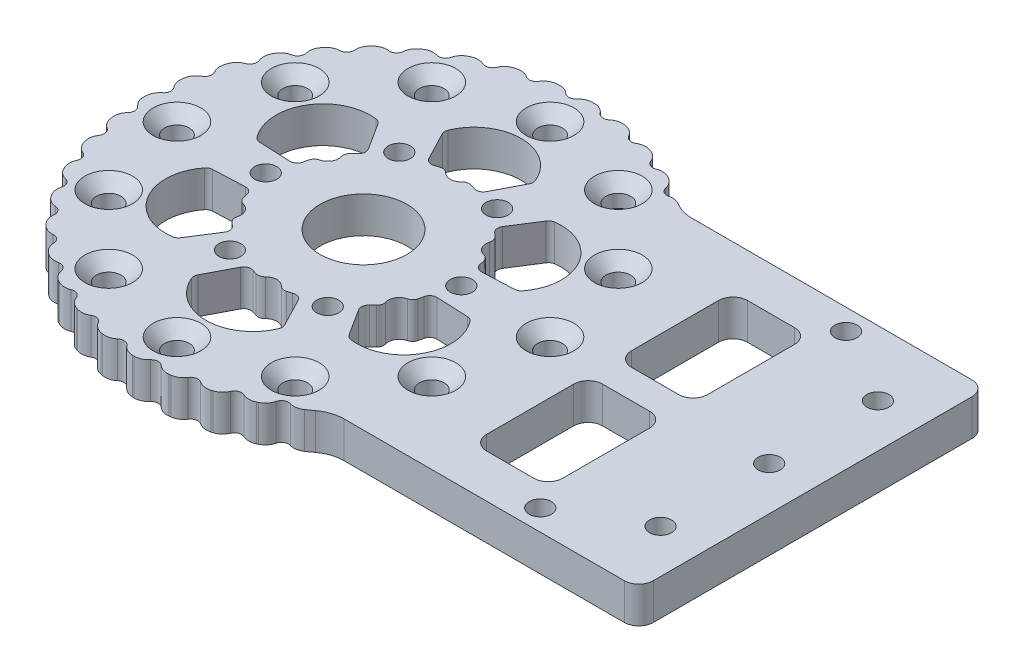
SolidWorks part; units mm, degrees
material "Thornel Mat VMA"
ref_plane "前视基准面" through (0, 0, 0) normal (0, 0, 1) x (1, 0, 0)
ref_plane "上视基准面" through (0, 0, 0) normal (0, 1, 0) x (1, 0, 0)
ref_plane "右视基准面" through (0, 0, 0) normal (1, 0, 0) x (0, 0, -1)
other "Configuration Table"
sketch "草图1" plane through (0, 0, 0) normal (0, 1, 0) x (1, 0, 0)
  line L1 (-105, -24) -> (105, -24)
  line L2 (-105, -24) -> (-105, 24) construction
  line L3 (-105, 24) -> (105, 24)
  line L4 (105, -24) -> (105, 24)
  line L5 (-105, -24) -> (105, 24) construction
  line L6 (-105, 24) -> (105, -24) construction
  circle A0 centre (105, 0) radius 24
  circle A1 centre (-105, 0) radius 37
  point P0 (0, 0)
  dimension "D1" = 48
  dimension "D3" = 74
  dimension "D2" = 210
extrude "凸台-拉伸1" add sketch "草图1" along normal blind 5
sketch "草图2" plane through (0, 0, 0) normal (0, -1, 0) x (1, 0, 0)
  line L0 (118.435, 13.435) -> (105, 0) construction
  line L1 (105, 0) -> (129, 0) construction
  circle A0 centre (105, 0) radius 19 construction
  circle A1 centre (118.435, 13.435) radius 1.275
  arc A2 (105, -24) -> (105, 24) centre (105, 0) ccw construction
  circle A3 centre (118.435, -13.435) radius 1.275
  circle A4 centre (91.565, -13.435) radius 1.275
  circle A5 centre (91.565, 13.435) radius 1.275
  circle A6 centre (124, 0) radius 1.275
  circle A7 centre (105, -19) radius 1.275
  circle A8 centre (86, 0) radius 1.275
  circle A9 centre (105, 19) radius 1.275
  point P18 (105, 0)
  point P26 (105, 0)
  dimension "D1" = 38
  dimension "D3" = 2.55
  dimension "D4" = 4
  dimension "D2" = 45
  dimension "D5" = 4
extrude "切除-拉伸1" cut sketch "草图2" against normal through all
sketch "草图3" plane through (0, 5, 0) normal (0, 1, 0) x (1, 0, 0)
  circle A16 centre (-105, 0) radius 17.25 construction
  circle A17 centre (-105, 17.25) radius 2.025
  circle A18 centre (-90.0611, 8.625) radius 2.025
  circle A19 centre (-90.0611, -8.625) radius 2.025
  circle A20 centre (-105, -17.25) radius 2.025
  circle A21 centre (-119.9389, -8.625) radius 2.025
  circle A22 centre (-119.9389, 8.625) radius 2.025
  point P18 (-105, 0)
  dimension "D1" = 34.5
  dimension "D2" = 4.05
sketch "草图5" plane through (0, 5, 0) normal (0, 1, 0) x (1, 0, 0)
  circle A0 centre (-105, 0) radius 10
  dimension "D1" = 20
extrude "切除-拉伸3" cut sketch "草图5" against normal through all
sketch "草图6" plane through (0, 5, 0) normal (0, 1, 0) x (1, 0, 0)
  circle A0 centre (-105, 0) radius 30 construction
  circle A1 centre (-135, 0) radius 1.525
  circle A2 centre (-120, 25.9808) radius 1.525
  circle A3 centre (-90, 25.9808) radius 1.525
  circle A4 centre (-75, 0) radius 1.525
  circle A5 centre (-90, -25.9808) radius 1.525
  circle A6 centre (-120, -25.9808) radius 1.525
  point P17 (-105, 0)
  dimension "D1" = 60
  dimension "D2" = 3.05
  dimension "D3" = 6
extrude "切除-拉伸4" cut sketch "草图6" against normal through all
sketch "草图7" plane through (0, 5, 0) normal (0, 1, 0) x (1, 0, 0)
  line L0 (-76.8397, 24) -> (105, 24) construction
  line L1 (0, 0) -> (50000, 0) construction
  circle A0 centre (-60, 19) radius 1.525
  circle A1 centre (-27, 19) radius 1.525
  circle A2 centre (6, 19) radius 1.525
  circle A3 centre (39, 19) radius 1.525
  circle A4 centre (72, 19) radius 1.525
  circle A5 centre (72, -19) radius 1.525
  circle A6 centre (39, -19) radius 1.525
  circle A7 centre (6, -19) radius 1.525
  circle A8 centre (-27, -19) radius 1.525
  circle A9 centre (-60, -19) radius 1.525
  dimension "D1" = 3.05
  dimension "D2" = 5
  dimension "D3" = 60
  dimension "D5" = 33
  dimension "D4" = 5
sketch "草图8" plane through (0, 0, 0) normal (0, -1, 0) x (1, 0, 0)
  line L0 (-44.8493, 17.0002) -> (-34.9998, 17.0002) construction
  line L1 (-32.9998, -3.6043) -> (-32.9998, 15.0002) construction
  line L2 (-46.6169, 14.0644) -> (-36.7674, -4.5401) construction
  line L3 (-48.9998, -16.9998) -> (-39.1504, -16.9998) construction
  line L5 (-47.2322, 4.5405) -> (-37.3828, -14.064) construction
  line L6 (-50.9998, -14.9998) -> (-50.9998, 3.6048) construction
  line L7 (-44.8493, 17.0002) -> (-34.9998, 17.0002)
  line L13 (-32.9998, -3.6043) -> (-32.9998, 15.0002)
  line L14 (-46.6169, 14.0644) -> (-36.7674, -4.5401)
  line L15 (-48.9998, -16.9998) -> (-39.1504, -16.9998)
  line L21 (-47.2322, 4.5405) -> (-37.3828, -14.064)
  line L22 (-50.9998, -14.9998) -> (-50.9998, 3.6048)
  arc A0 (-44.8493, 17.0002) -> (-46.6169, 14.0644) centre (-44.8493, 15.0002) ccw construction
  arc A1 (-32.9998, 15.0002) -> (-34.9998, 17.0002) centre (-34.9998, 15.0002) ccw construction
  arc A2 (-36.7674, -4.5401) -> (-32.9998, -3.6043) centre (-34.9998, -3.6043) ccw construction
  arc A3 (-39.1504, -16.9998) -> (-37.3828, -14.064) centre (-39.1504, -14.9998) ccw construction
  arc A36 (-50.9998, -14.9998) -> (-48.9998, -16.9998) centre (-48.9998, -14.9998) ccw construction
  arc A37 (-47.2322, 4.5405) -> (-50.9998, 3.6048) centre (-48.9998, 3.6048) ccw construction
  arc A38 (-44.8493, 17.0002) -> (-46.6169, 14.0644) centre (-44.8493, 15.0002) ccw
  arc A39 (-32.9998, 15.0002) -> (-34.9998, 17.0002) centre (-34.9998, 15.0002) ccw
  arc A40 (-36.7674, -4.5401) -> (-32.9998, -3.6043) centre (-34.9998, -3.6043) ccw
  arc A41 (-39.1504, -16.9998) -> (-37.3828, -14.064) centre (-39.1504, -14.9998) ccw
  arc A42 (-50.9998, -14.9998) -> (-48.9998, -16.9998) centre (-48.9998, -14.9998) ccw
  arc A43 (-47.2322, 4.5405) -> (-50.9998, 3.6048) centre (-48.9998, 3.6048) ccw
sketch "草图9" plane through (0, 0, 0) normal (0, -1, 0) x (1, 0, 0)
  circle A0 centre (105, 0) radius 12.5
  dimension "D1" = 25
extrude "切除-拉伸7" cut sketch "草图9" against normal through all
hole_wizard "M3 十字槽沉头木螺钉的锥形沉头孔1" positions "草图10" profile "草图11" countersink size "M3" standard "GB" end condition through all
sketch "草图10" plane through (0, 5, 0) normal (0, 1, 0) x (1, 0, 0)
  point P0 (105, 19)
sketch "草图11" plane through (105, 5, -19) normal (1, 0, 0) x (0, 0, 1)
  line L0 (0, 0) -> (0, 5)
  line L1 (0, 5) -> (1.8, 5)
  line L2 (1.8, 5) -> (1.8, 1.5)
  line L3 (1.8, 1.5) -> (3.3, 0)
  line L5 (3.3, 0) -> (0, 0)
  line L6 (-1.8, 1.5) -> (-3.3, 0) construction
  line L11 (0, -6.35) -> (0, 107.95) construction
  dimension "通孔孔直径" = 3.6
  dimension "通孔孔深度" = 5
  dimension "近端锥形沉头孔直径" = 6.6
  dimension "近端锥形沉头孔角度" = 90
hole_wizard "孔1" positions "草图12" profile "草图13" legacy end condition through all
sketch "草图12" plane through (0, 5, 0) normal (0, 1, 0) x (1, 0, 0)
  point P0 (91.565, 13.435)
  point P3 (86, 0)
  point P6 (91.565, -13.435)
  point P9 (105, -19)
  point P12 (118.435, -13.435)
  point P15 (124, 0)
  point P18 (118.435, 13.435)
sketch "草图13" plane through (91.565, 5, -13.435) normal (1, 0, 0) x (0, 0, 1)
  line L0 (0, 0) -> (0, 5)
  line L1 (0, 5) -> (1.5, 5)
  line L2 (1.5, 5) -> (1.5, 1.5)
  line L3 (1.5, 1.5) -> (3, 0)
  line L4 (3, 0) -> (0, 0)
  line L5 (0, -6.4453) -> (0, 115.525) construction
  line L6 (-1.5, 1.5) -> (-3, 0) construction
  dimension "直径" = 3
  dimension "深度" = 5
  dimension "锥坑角度" = 90
  dimension "锥坑直径" = 6
extrude "切除-拉伸8" cut sketch "草图3" against normal blind 10
sketch "草图14" plane through (0, 5, 0) normal (0, 1, 0) x (1, 0, 0)
  circle A0 centre (-105, 0) radius 37
  arc A1 (-76.8397, 24) -> (-76.8397, -24) centre (-105, 0) ccw construction
extrude "凸台-拉伸2" add sketch "草图14" against normal up to surface (5 mm away) up to face at (-105, 0, -15.225)
sketch "草图15" plane through (0, 5, 0) normal (0, 1, 0) x (1, 0, 0)
  circle A0 centre (-105, 0) radius 42.5
  dimension "D1" = 85
extrude "凸台-拉伸3" add sketch "草图15" against normal up to surface (5 mm away) up to face at (91.565, 0, -11.935)
sketch "草图16" plane through (0, 0, 0) normal (0, -1, 0) x (1, 0, 0)
  circle A0 centre (-105, 0) radius 13.5 construction
  circle A1 centre (-105, 13.5) radius 1.525
  circle A2 centre (-98.25, 11.6913) radius 1.525
  circle A3 centre (-93.3087, 6.75) radius 1.525
  circle A4 centre (-91.5, 0) radius 1.525
  circle A5 centre (-93.3087, -6.75) radius 1.525
  circle A6 centre (-98.25, -11.6913) radius 1.525
  circle A7 centre (-105, -13.5) radius 1.525
  circle A8 centre (-111.75, -11.6913) radius 1.525
  circle A9 centre (-116.6913, -6.75) radius 1.525
  circle A10 centre (-118.5, 0) radius 1.525
  circle A11 centre (-116.6913, 6.75) radius 1.525
  circle A12 centre (-111.75, 11.6913) radius 1.525
  point P22 (-105, 0)
  dimension "D1" = 27
  dimension "D2" = 3.05
  dimension "D3" = 12
extrude "切除-拉伸9" cut sketch "草图16" against normal up to surface (5 mm away) up to face at (4.1437, 5, 0)
sketch "草图18" plane through (0, 5, 0) normal (0, 1, 0) x (1, 0, 0)
  line L0 (-98.8153, 17.25) -> (-101.4581, 12.1732)
  line L1 (-111.1847, 17.25) -> (-108.5419, 12.1732)
  line L2 (-105, 0) -> (-105, -17.25) construction
  circle A0 centre (-105, 0) radius 17.25 construction
  circle A1 centre (-105, 17.25) radius 3.8 construction
  circle A2 centre (-90.0611, 8.625) radius 3.8 construction
  circle A3 centre (-90.0611, -8.625) radius 3.8 construction
  circle A4 centre (-105, -17.25) radius 3.8 construction
  circle A5 centre (-119.9389, -8.625) radius 3.8 construction
  circle A6 centre (-119.9389, 8.625) radius 3.8 construction
  arc A7 (-111.1847, 17.25) -> (-98.8153, 17.25) centre (-105, 15.25) cw
  arc A8 (-108.5419, 12.1732) -> (-101.4581, 12.1732) centre (-105, 5) cw
  point P17 (-105, 0)
  dimension "D1" = 34.5
  dimension "D2" = 7.6
  dimension "D5" = 6.5
  dimension "D7" = 8
  dimension "D4" = 2
  dimension "D6" = 5
  dimension "D8" = 55
  dimension "D3" = 6
extrude "切除-拉伸10" cut sketch "草图18" against normal up to surface (5 mm away) up to face at (-111.75, 0, -13.2163)
pattern_circular "阵列(圆周)1" count 6 over 360 about axis through (-105, 0, 0) along (0, 1, 0) of "切除-拉伸10"
sketch "草图19" plane through (0, 0, 0) normal (0, -1, 0) x (1, 0, 0)
  circle A0 centre (-105, 0) radius 6
  dimension "D1" = 12
extrude "切除-拉伸11" cut sketch "草图19" against normal up to surface (5 mm away) up to face at (-92.2475, 5, -7.3627)
sketch "草图20" plane through (0, 0, 0) normal (0, -1, 0) x (1, 0, 0)
  circle A10 centre (-105, 0) radius 36.75 construction
  circle A11 centre (-68.25, 0) radius 1.525
  circle A12 centre (-79.0138, -25.9862) radius 1.525
  circle A13 centre (-105, -36.75) radius 1.525
  circle A14 centre (-130.9862, -25.9862) radius 1.525
  circle A15 centre (-141.75, 0) radius 1.525
  circle A16 centre (-130.9862, 25.9862) radius 1.525
  circle A17 centre (-105, 36.75) radius 1.525
  circle A18 centre (-79.0138, 25.9862) radius 1.525
  point P21 (-105, 0)
  dimension "D1" = 73.5
  dimension "D2" = 3.05
fillet "圆角1" radius 2 2 edges at (-69.9251, 2.5, -24) (-69.9251, 2.5, 24)
sketch "草图21" plane through (0, 0, 0) normal (0, -1, 0) x (1, 0, 0)
  line L0 (-68.8856, -24) -> (105, -24) construction
  line L1 (-68.8856, 24) -> (105, 24) construction
  line L2 (-68.8856, -24) -> (105, -24)
  line L3 (-68.8856, 24) -> (105, 24)
  line L4 (-68.8856, 24) -> (-85.3786, 24)
  line L5 (-68.8856, -24) -> (-85.3786, -24)
  line L8 (105, 24) -> (-68.8856, 24)
  line L9 (-68.8856, -24) -> (105, -24)
  line L10 (105, 24) -> (-68.8856, 24)
  line L11 (-68.8856, -24) -> (105, -24)
  circle A0 centre (-105, 0) radius 31
  arc A3 (-70.5087, 24.8315) -> (-68.8856, 24) centre (-68.8856, 26) ccw
  arc A7 (-70.5087, 24.8315) -> (-68.8856, 24) centre (-68.8856, 26) ccw
  arc A8 (105, -24) -> (105, 24) centre (105, 0) ccw
  arc A12 (105, -24) -> (105, 24) centre (105, 0) ccw
  arc A13 (-70.5087, 24.8315) -> (-70.5087, -24.8315) centre (-105, 0) ccw
  arc A14 (-70.5087, 24.8315) -> (-70.5087, -24.8315) centre (-105, 0) ccw
  arc A15 (-68.8856, -24) -> (-70.5087, -24.8315) centre (-68.8856, -26) ccw
  arc A16 (-68.8856, -24) -> (-70.5087, -24.8315) centre (-68.8856, -26) ccw
  dimension "D1" = 62
  dimension "D2" = 0
extrude "切除-拉伸13" cut sketch "草图21" against normal through all contours A16 L5 A0 L4 A7 A14
fillet "圆角2" radius 1 36 edges at (-94.5436, 2.5, -7.6448) (-93.1512, 2.5, -5.2331) (-96.2286, 2.5, -9.154) (-93.1534, 2.5, -13.9811) (-86.9687, 2.5, -3.2689) (-92.6867, 2.5, -3.0193) (-93.1512, 2.5, 5.2331) (-94.5436, 2.5, 7.6448) (-92.6867, 2.5, 3.0193) (-86.9687, 2.5, 3.2689) (-93.1534, 2.5, 13.9811) (-96.2286, 2.5, 9.154) (-103.6077, 2.5, 12.8779) (-106.3923, 2.5, 12.8779) (-101.4581, 2.5, 12.1732) (-98.8153, 2.5, 17.25) (-111.1847, 2.5, 17.25) (-108.5419, 2.5, 12.1732) (-115.4564, 2.5, 7.6448) (-116.8488, 2.5, 5.2331) (-113.7714, 2.5, 9.154) (-123.0313, 2.5, 3.2689) (-117.3133, 2.5, 3.0193) (-116.8488, 2.5, -5.2331) (-115.4564, 2.5, -7.6448) (-117.3133, 2.5, -3.0193) (-123.0313, 2.5, -3.2689) (-116.8466, 2.5, -13.9811) (-113.7714, 2.5, -9.154) (-106.3923, 2.5, -12.8779) (-103.6077, 2.5, -12.8779) (-108.5419, 2.5, -12.1732) (-111.1847, 2.5, -17.25) (-98.8153, 2.5, -17.25) (-101.4581, 2.5, -12.1732) (-116.8466, 2.5, 13.9811)
sketch "草图22" plane through (0, 0, 0) normal (0, -1, 0) x (1, 0, 0)
  line L0 (-35, 24) -> (-35, -24)
  line L1 (-85.3786, 24) -> (105, 24) construction
  line L2 (-85.3786, -24) -> (105, -24) construction
  line L4 (-35, 24) -> (145, 24)
  line L5 (-35, 24) -> (-35, -24)
  line L6 (-35, -24) -> (145, -24)
  line L7 (145, 24) -> (145, -24)
  arc A0 (105, -24) -> (105, 24) centre (105, 0) ccw construction
  dimension "D1" = 140
  dimension "D2" = 180
extrude "切除-拉伸14" cut sketch "草图22" against normal through all contours L7 L4 L0 L6
sketch "草图23" plane through (0, 0, 0) normal (0, -1, 0) x (1, 0, 0)
  line L0 (-105, 0) -> (-105, 50000) construction
  line L1 (-117.875, 22.3002) -> (24882.125, -43278.97) construction
  circle A0 centre (-105, 0) radius 25.75 construction
  circle A1 centre (-117.875, 22.3002) radius 1.525
  circle A2 centre (-105, 25.75) radius 1.525
  circle A3 centre (-92.125, 22.3002) radius 1.525
  circle A4 centre (-82.6998, 12.875) radius 1.525
  circle A5 centre (-79.25, 0) radius 1.525
  circle A6 centre (-82.6998, -12.875) radius 1.525
  circle A7 centre (-92.125, -22.3002) radius 1.525
  circle A8 centre (-105, -25.75) radius 1.525
  circle A9 centre (-117.875, -22.3002) radius 1.525
  circle A10 centre (-127.3002, -12.875) radius 1.525
  circle A11 centre (-130.75, 0) radius 1.525
  circle A12 centre (-127.3002, 12.875) radius 1.525
  point P23 (-105, 0)
  dimension "D1" = 51.5
  dimension "D2" = 3.05
  dimension "D3" = 30
  dimension "D4" = 12
extrude "切除-拉伸15" cut sketch "草图23" against normal through all
sketch "草图27" plane through (0, 0, 0) normal (0, -1, 0) x (1, 0, 0)
  line L0 (-38, 24) -> (-38, 50024) construction
  line L2 (-35, 24) -> (-35, -24) construction
  line L3 (-38, 0) -> (49962, 0) construction
  circle A0 centre (-38, 0) radius 1.525
  circle A1 centre (-38, 20) radius 1.525
  circle A2 centre (-38, -20) radius 1.525
  dimension "D2" = 3.05
  dimension "D4" = 3.05
  dimension "D1" = 3
  dimension "D3" = 20
extrude "切除-拉伸16" cut sketch "草图27" against normal through all
sketch "草图28" plane through (0, 0, 0) normal (0, -1, 0) x (1, 0, 0)
  line L0 (-35, 24) -> (-35, -24) construction
  line L1 (-72, -18) -> (-47, -18)
  line L2 (-72, -18) -> (-72, 18)
  line L3 (-72, 18) -> (-47, 18)
  line L4 (-47, -18) -> (-47, 18)
  line L5 (-72, -18) -> (-47, 18) construction
  line L6 (-72, 18) -> (-47, -18) construction
  line L7 (-72, 0) -> (-47, 0) construction
  line L8 (-59.5, 18) -> (-59.5, -18) construction
  line L9 (-61.5, 18) -> (-61.5, -18)
  line L10 (-72, -2) -> (-47, -2)
  line L11 (-57.5, 18) -> (-57.5, -18)
  line L12 (-72, 2) -> (-47, 2)
  point P0 (-59.5, 0)
  dimension "D1" = 36
  dimension "D2" = 12
  dimension "D3" = 25
  dimension "D4" = 2
  dimension "D5" = 2
extrude "切除-拉伸17" cut sketch "草图28" against normal through all contours L2 L12 L9 L3 | L10 L2 L1 L9
fillet "圆角3" radius 2 4 edges at (-61.5, 2.5, 18) (-61.5, 2.5, 2) (-72, 2.5, 2) (-72, 2.5, 18)
fillet "圆角5" radius 2 2 edges at (-35, 2.5, -24) (-35, 2.5, 24)
fillet "圆角6" radius 5 2 edges at (-85.3786, 2.5, -24) (-85.3786, 2.5, 24)
sketch "草图30" plane through (0, 0, 0) normal (0, -1, 0) x (1, 0, 0)
  line L0 (-113.0234, 29.9437) -> (-105, 0) construction
  line L1 (-105, 0) -> (-105, 31) construction
  circle A0 centre (-113.0234, 29.9437) radius 1
  arc A1 (-86.6319, 24.9722) -> (-86.6319, -24.9722) centre (-105, 0) ccw construction
  dimension "D2" = 2
  dimension "D1" = 15
extrude "切除-拉伸18" cut sketch "草图30" against normal through all
pattern_circular "阵列(圆周)2" count 40 over 360 about axis through (-105, 0, 0) along (0, 1, 0) skipping 23, 24, 25, 26, 27, 28, 29, 30, 31, 32, 33, 34 of "切除-拉伸18"
fillet "圆角7" radius 2 56 edges at (-110.4639, 2.5, -30.5147) (-112.4199, 2.5, -30.0989) (-115.1702, 2.5, -29.2843) (-117.0371, 2.5, -28.5676) (-119.626, 2.5, -27.3328) (-121.3578, 2.5, -26.3329) (-123.7217, 2.5, -24.7082) (-125.2758, 2.5, -23.4498) (-127.3565, 2.5, -21.4753) (-128.6945, 2.5, -19.9892) (-130.4407, 2.5, -17.7136) (-131.5298, 2.5, -16.0365) (-132.8985, 2.5, -13.5157) (-133.7119, 2.5, -11.6888) (-134.6693, 2.5, -8.985) (-135.1869, 2.5, -7.0534) (-135.7096, 2.5, -4.2331) (-135.9187, 2.5, -2.2443) (-135.9937, 2.5, 0.6231) (-135.8891, 2.5, 2.6201) (-135.5147, 2.5, 5.4639) (-135.0989, 2.5, 7.4199) (-134.2843, 2.5, 10.1702) (-133.5676, 2.5, 12.0371) (-132.3328, 2.5, 14.626) (-131.3329, 2.5, 16.3578) (-129.7082, 2.5, 18.7217) (-128.4498, 2.5, 20.2758) (-126.4753, 2.5, 22.3565) (-124.9892, 2.5, 23.6945) (-122.7136, 2.5, 25.4407) (-121.0365, 2.5, 26.5298) (-118.5157, 2.5, 27.8985) (-116.6888, 2.5, 28.7119) (-113.985, 2.5, 29.6693) (-112.0534, 2.5, 30.1869) (-109.2331, 2.5, 30.7096) (-107.2443, 2.5, 30.9187) (-104.3769, 2.5, 30.9937) (-102.3799, 2.5, 30.8891) (-99.5361, 2.5, 30.5147) (-97.5801, 2.5, 30.0989) (-94.8298, 2.5, 29.2843) (-92.9629, 2.5, 28.5676) (-90.374, 2.5, 27.3328) (-88.6422, 2.5, 26.3329) (-87.2864, 2.5, -25.4407) (-88.9635, 2.5, -26.5298) (-91.4843, 2.5, -27.8985) (-93.3112, 2.5, -28.7119) (-96.015, 2.5, -29.6693) (-97.9466, 2.5, -30.1869) (-100.7669, 2.5, -30.7096) (-102.7557, 2.5, -30.9187) (-105.6231, 2.5, -30.9937) (-107.6201, 2.5, -30.8891)
sketch "草图31" plane through (0, 0, 0) normal (0, -1, 0) x (1, 0, 0)
  line L0 (-59.5, 11.4408) -> (-59.5, 50011.4408) construction
  line L1 (-35, 22) -> (-35, -22) construction
  line L2 (-83.6693, 24) -> (-37, 24) construction
  line L3 (-38, 0) -> (49962, 0) construction
  circle A0 centre (-59.5, 21.1) radius 1.525
  circle A1 centre (-59.5, -21.1) radius 1.525
  dimension "D3" = 3.05
  dimension "D1" = 24.5
  dimension "D2" = 2.9
extrude "切除-拉伸19" cut sketch "草图31" against normal through all
sketch "草图32" plane through (0, 0, 0) normal (0, -1, 0) x (1, 0, 0)
  line L0 (-49, 24) -> (-49, 50024) construction
  line L2 (-49.5, 0) -> (49950.5, 0) construction
  circle A0 centre (-105, 0) radius 6 construction
  circle A1 centre (-49, 0) radius 1.525
  circle A2 centre (-49, 15) radius 1.525
  circle A3 centre (-49, -15) radius 1.525
  dimension "D1" = 56
  dimension "D2" = 3.05
  dimension "D3" = 15
extrude "切除-拉伸20" cut sketch "草图32" against normal through all
sketch "草图33" plane through (0, 0, 0) normal (0, -1, 0) x (1, 0, 0)
  line L0 (-83.6693, 24) -> (-37, 24) construction
  line L1 (-43, 24) -> (19, 24)
  line L2 (-43, 24) -> (-43, -26.1341)
  line L3 (-43, -26.1341) -> (19, -26.1341)
  line L4 (19, 24) -> (19, -26.1341)
  circle A0 centre (-105, 0) radius 6 construction
  dimension "D1" = 62
  dimension "D2" = 62
  dimension "D3" = 50.1341
extrude "切除-拉伸21" cut sketch "草图33" against normal through all
fillet "圆角8" radius 2 4 edges at (-61.5, 2.5, -18) (-72, 2.5, -18) (-72, 2.5, -2) (-61.5, 2.5, -2)
fillet "圆角9" radius 2 2 edges at (-43, 2.5, -24) (-43, 2.5, 24)
sketch "草图35" plane through (0, 0, 0) normal (0, -1, 0) x (-1, 0, 0)
  point P0 (92.125, 22.3002)
hole_wizard "M3 开槽半沉头木螺钉的锥形沉头孔1" positions "草图35" profile "草图36" countersink size "M3" standard "GB" end condition through all
sketch "草图36" plane through (-92.125, 0, -22.3002) normal (1, 0, 0) x (0, 0, -1)
  line L0 (0, 0) -> (0, 5)
  line L1 (0, 5) -> (1.7, 5)
  line L2 (1.7, 5) -> (1.7, 1.6)
  line L3 (1.7, 1.6) -> (3.3, 0)
  line L5 (3.3, 0) -> (0, 0)
  line L6 (-1.7, 1.6) -> (-3.3, 0) construction
  line L11 (0, -6.35) -> (0, 107.95) construction
  dimension "通孔孔直径" = 3.4
  dimension "通孔孔深度" = 5
  dimension "近端锥形沉头孔直径" = 6.6
  dimension "近端锥形沉头孔角度" = 90
sketch "草图37" plane through (0, 5, 0) normal (0, 1, 0) x (1, 0, 0)
  point P0 (-105, 25.75)
  point P3 (-92.125, 22.3002)
  point P6 (-117.875, 22.3002)
  point P9 (-127.3002, 12.875)
  point P12 (-130.75, 0)
  point P15 (-127.3002, -12.875)
  point P18 (-117.875, -22.3002)
  point P21 (-105, -25.75)
  point P24 (-92.125, -22.3002)
  point P27 (-82.6998, -12.875)
  point P30 (-79.25, 0)
  point P33 (-82.6998, 12.875)
hole_wizard "M3 开槽半沉头木螺钉的锥形沉头孔2" positions "草图37" profile "草图38" countersink size "M3" standard "GB" end condition through all
sketch "草图38" plane through (-105, 5, -25.75) normal (1, 0, 0) x (0, 0, 1)
  line L0 (0, 0) -> (0, 5)
  line L1 (0, 5) -> (1.7, 5)
  line L2 (1.7, 5) -> (1.7, 1.6)
  line L3 (1.7, 1.6) -> (3.3, 0)
  line L5 (3.3, 0) -> (0, 0)
  line L6 (-1.7, 1.6) -> (-3.3, 0) construction
  line L11 (0, -6.35) -> (0, 107.95) construction
  dimension "通孔孔直径" = 3.4
  dimension "通孔孔深度" = 5
  dimension "近端锥形沉头孔直径" = 6.6
  dimension "近端锥形沉头孔角度" = 90
